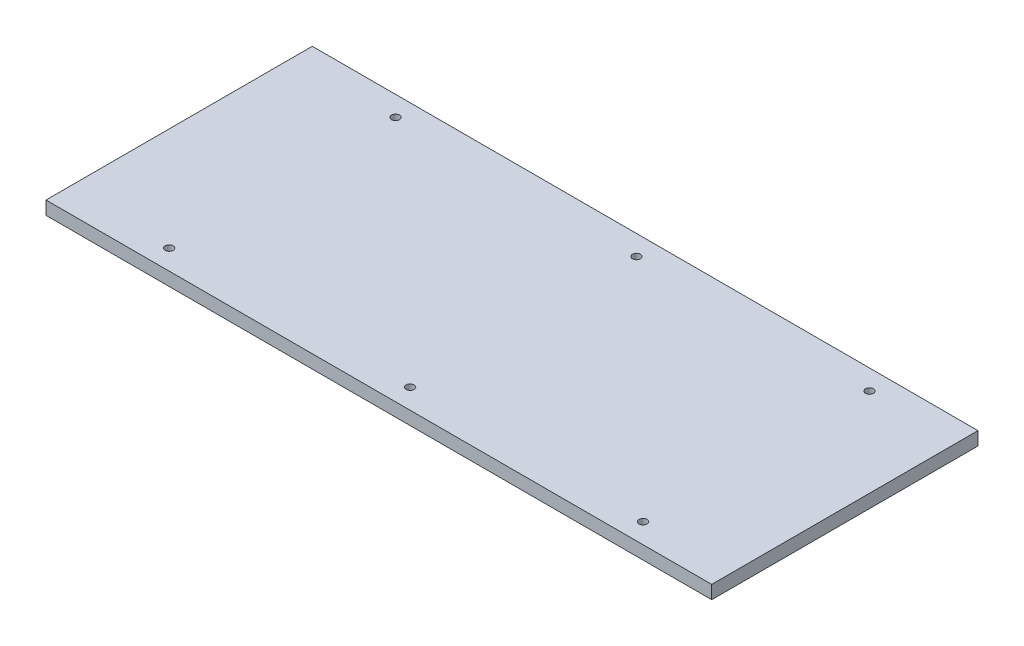
SolidWorks part; units mm, degrees
ref_plane "Front Plane" through (0, 0, 0) normal (0, 0, 1) x (1, 0, 0)
ref_plane "Top Plane" through (0, 0, 0) normal (0, 1, 0) x (1, 0, 0)
ref_plane "Right Plane" through (0, 0, 0) normal (1, 0, 0) x (0, 0, -1)
sketch "Sketch1" plane through (0, 0, 0) normal (0, 1, 0) x (1, 0, 0)
  line L1 (250, -100) -> (-250, -100)
  line L2 (250, -100) -> (250, 100)
  line L3 (250, 100) -> (-250, 100)
  line L4 (-250, -100) -> (-250, 100)
  circle A0 centre (8.4933, 85) radius 3
  circle A1 centre (8.4933, -85) radius 3
  circle A2 centre (-172.5067, 85) radius 3
  circle A3 centre (-172.5067, -85) radius 3
  circle A4 centre (183.4933, -85) radius 3
  circle A5 centre (183.4933, 85) radius 3
  point P0 (0, 0)
  dimension "D1" = 6
  dimension "D2" = 6
  dimension "D3" = 6
  dimension "D4" = 6
  dimension "D5" = 6
  dimension "D6" = 6
  dimension "D8" = 175
  dimension "D9" = 181
  dimension "D10" = 175
  dimension "D11" = 170
  dimension "D16" = 170
  dimension "D17" = 170
  dimension "D19" = 85
  dimension "D20" = 85
  dimension "D7" = 181
  dimension "D12" = 200
  dimension "D13" = 100
  dimension "D14" = 500
  dimension "D15" = 250
  dimension "D18" = 0
  dimension "D21" = 85
extrude "Boss-Extrude1" add sketch "Sketch1" along normal blind 10
